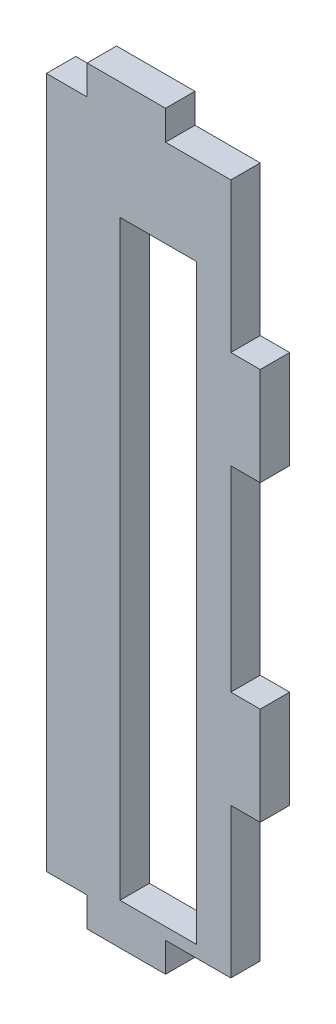
SolidWorks part; units mm, degrees
ref_plane "Front Plane" through (0, 0, 0) normal (0, 0, 1) x (1, 0, 0)
ref_plane "Top Plane" through (0, 0, 0) normal (0, 1, 0) x (1, 0, 0)
ref_plane "Right Plane" through (0, 0, 0) normal (1, 0, 0) x (0, 0, -1)
sketch "Sketch1" plane through (0, 0, 0) normal (0, 0, 1) x (1, 0, 0)
  line L0 (0, -10.75) -> (0, -24) construction
  line L2 (3, -10.75) -> (3, -0.75)
  line L5 (3, -29) -> (-24.3118, 47.5) construction
  line L6 (3, 47.5) -> (-24.3118, -29) construction
  line L7 (3, -10.75) -> (0, -10.75) construction
  line L8 (0, -10.75) -> (0, -24)
  line L9 (3, -10.75) -> (0, -10.75)
  line L10 (3, -0.75) -> (0, -0.75) construction
  line L11 (0, 19.25) -> (0, -0.75) construction
  line L12 (3, 19.25) -> (0, 19.25) construction
  line L13 (3, 29.25) -> (0, 29.25) construction
  line L14 (0, 42.5) -> (0, 29.25) construction
  line L15 (0, 47.5) -> (0, 42.5) construction
  line L16 (0, -24) -> (0, -29) construction
  line L17 (0, -24) -> (0, -26)
  line L18 (0, 44.5) -> (0, 42.5)
  line L19 (0, 42.5) -> (0, 29.25)
  line L20 (3, 29.25) -> (0, 29.25)
  line L21 (3, 19.25) -> (0, 19.25)
  line L22 (0, 19.25) -> (0, -0.75)
  line L23 (3, -0.75) -> (0, -0.75)
  line L24 (3, 19.25) -> (3, 29.25)
  line L25 (-10.6559, -35.4999) -> (-10.6559, 53.9999) construction
  line L26 (-3.5, -24.785) -> (-3.5, 35.54) construction
  line L36 (-3.5, 35.54) -> (-11.3, 35.54) construction
  line L37 (-11.3, -24.785) -> (-11.3, 35.54) construction
  line L38 (-3.5, -24.785) -> (-11.3, -24.785) construction
  line L39 (-3.5, -24.785) -> (-3.5, 35.54)
  line L40 (-3.5, 35.54) -> (-11.3, 35.54)
  line L41 (-11.3, -24.785) -> (-11.3, 35.54)
  line L42 (-3.5, -24.785) -> (-11.3, -24.785)
  line L52 (0, -26) -> (-2, -26)
  line L53 (-19.3118, -26) -> (-21.3118, -26)
  line L54 (-19.3118, -26) -> (-2, -26)
  line L56 (0, 44.5) -> (-21.3118, 44.5)
  line L57 (-21.3118, -26) -> (-21.3118, 44.5)
  point P4 (-10.6559, 9.25)
  point P11 (0, 0)
  point P18 (-10.6559, 9.25)
  point P24 (3, -29)
extrude "Boss-Extrude1" add sketch "Sketch1" along normal blind 3
sketch "Sketch2" plane through (0, 0, 3) normal (0, 0, 1) x (1, 0, 0)
  line L0 (0, 44.5) -> (-21.3118, 44.5) construction
  line L1 (-21.3118, -26) -> (-18.8118, -26)
  line L2 (-21.3118, -26) -> (-21.3118, 44.5)
  line L3 (-21.3118, 44.5) -> (-18.8118, 44.5)
  line L4 (-18.8118, -26) -> (-18.8118, 44.5)
  line L5 (-21.3118, -26) -> (-18.8118, 44.5) construction
  line L6 (-21.3118, 44.5) -> (-18.8118, -26) construction
  point P4 (-20.0618, 9.25)
  dimension "D1" = 2.5
extrude "Cut-Extrude1" cut sketch "Sketch2" against normal blind 3
sketch "Sketch3" plane through (0, 0, 3) normal (0, 0, 1) x (1, 0, 0)
  line L0 (-14.6559, -26) -> (-14.6559, -29) construction
  line L1 (-6.6559, -26) -> (-6.6559, -29) construction
  line L2 (-14.6559, -26) -> (-14.6559, -29)
  line L3 (-6.6559, -26) -> (-6.6559, -29)
  line L4 (-6.6559, -26) -> (-14.6559, -26)
  line L5 (-6.6559, -29) -> (-14.6559, -29)
  line L6 (0, 9.25) -> (-36.8131, 9.25) construction
  line L7 (0, -0.75) -> (0, 19.25) construction
  line L8 (-6.6559, 47.5) -> (-14.6559, 47.5)
  line L9 (-6.6559, 44.5) -> (-14.6559, 44.5)
  line L10 (-6.6559, 44.5) -> (-6.6559, 47.5)
  line L11 (-14.6559, 44.5) -> (-14.6559, 47.5)
extrude "Boss-Extrude2" add sketch "Sketch3" against normal blind 3
